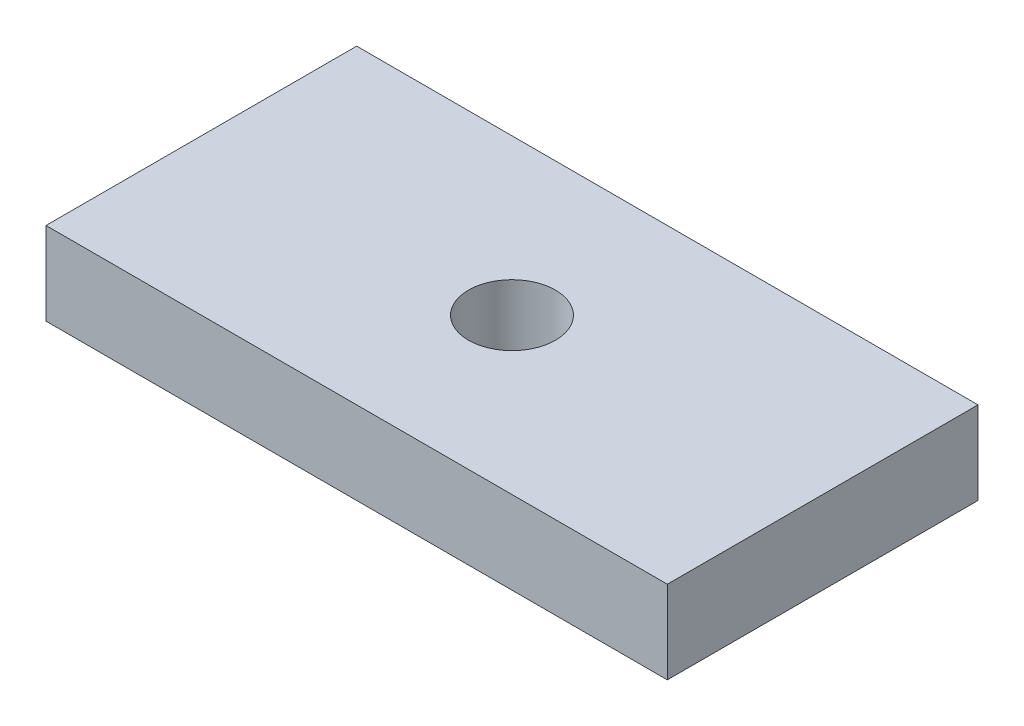
SolidWorks part; units mm, degrees
material "PVC hart"
ref_plane "Ebene vorne" through (0, 0, 0) normal (0, 0, 1) x (1, 0, 0)
ref_plane "Ebene oben" through (0, 0, 0) normal (0, 1, 0) x (1, 0, 0)
ref_plane "Ebene rechts" through (0, 0, 0) normal (1, 0, 0) x (0, 0, -1)
sketch "Skizze1" plane through (0, 0, 0) normal (0, 1, 0) x (1, 0, 0)
  line L1 (-15, 7.5) -> (15, 7.5)
  line L2 (-15, 7.5) -> (-15, -7.5)
  line L3 (-15, -7.5) -> (15, -7.5)
  line L4 (15, 7.5) -> (15, -7.5)
  line L5 (-15, 7.5) -> (15, -7.5) construction
  line L6 (-15, -7.5) -> (15, 7.5) construction
  circle A0 centre (0, 0) radius 2.1
  dimension "D1" = 4.2
  dimension "D2" = 15
  dimension "D3" = 30
extrude "Aufsatz-Linear austragen1" add sketch "Skizze1" along normal mid plane 4
